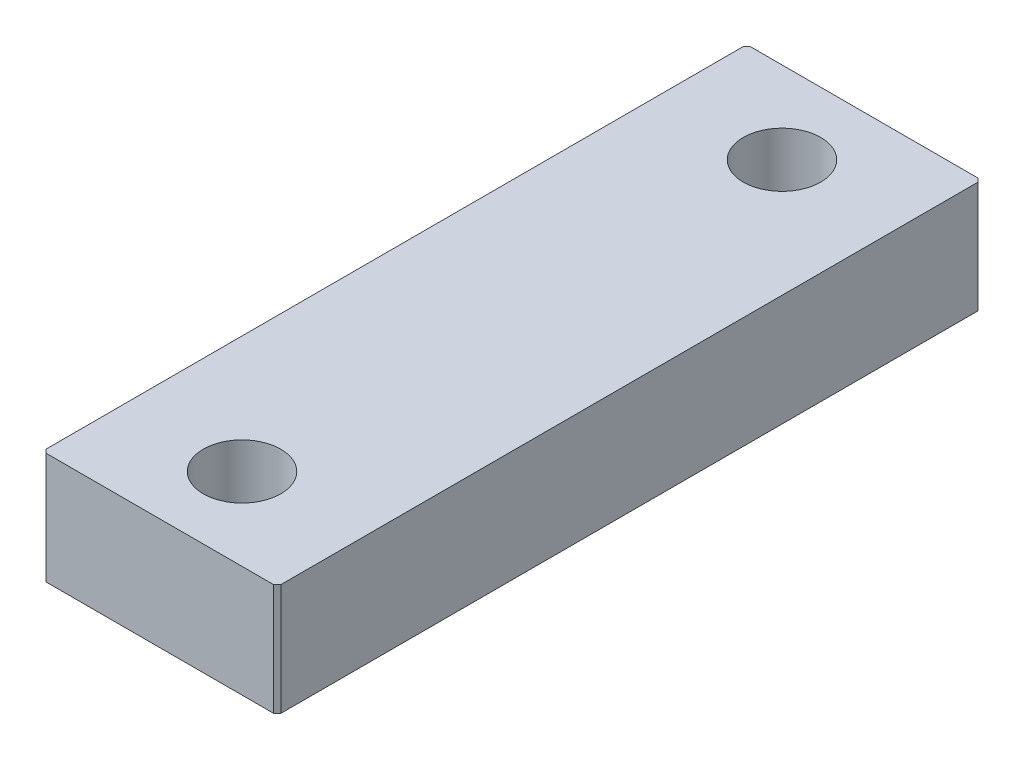
SolidWorks part; units mm, degrees
ref_plane "Front Plane" through (0, 0, 0) normal (0, 0, 1) x (1, 0, 0)
ref_plane "Top Plane" through (0, 0, 0) normal (0, 1, 0) x (1, 0, 0)
ref_plane "Right Plane" through (0, 0, 0) normal (1, 0, 0) x (0, 0, -1)
sketch "Sketch1" plane through (0, 0, 0) normal (0, 1, 0) x (1, 0, 0)
  line L0 (0, 23) -> (0, -23) construction
  line L1 (10, 30) -> (-10, 30)
  line L2 (10, 30) -> (10, -30)
  line L3 (10, -30) -> (-10, -30)
  line L4 (-10, 30) -> (-10, -30)
  line L5 (10, 30) -> (-10, -30) construction
  line L6 (10, -30) -> (-10, 30) construction
  circle A0 centre (0, 23) radius 3.3
  circle A1 centre (0, -23) radius 3.3
  point P0 (0, 0)
  dimension "D4" = 6.6
  dimension "D1" = 20
  dimension "D2" = 60
  dimension "D3" = 46
extrude "Boss-Extrude1" add sketch "Sketch1" along normal blind 9.5
chamfer "Chamfer1" distance 0.3 angle 45 4 edges at (10, 4.75, -30) (-10, 4.75, -30) (-10, 4.75, 30) (10, 4.75, 30)
